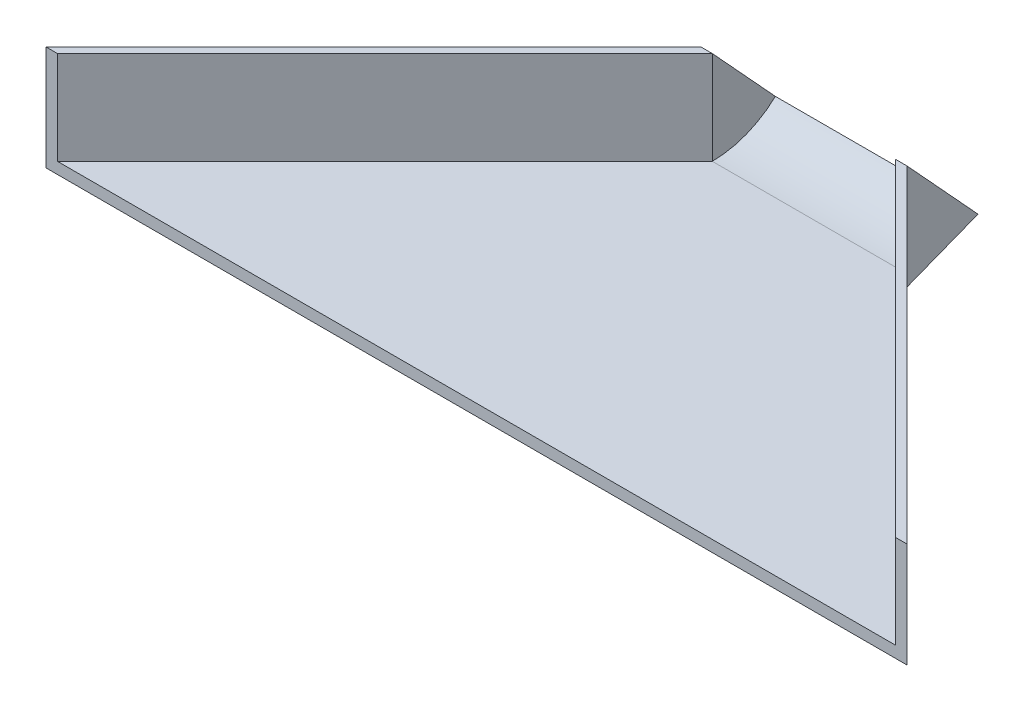
SolidWorks part; units mm, degrees
ref_plane "Front Plane" through (0, 0, 0) normal (0, 0, 1) x (1, 0, 0)
ref_plane "Top Plane" through (0, 0, 0) normal (0, 1, 0) x (1, 0, 0)
ref_plane "Right Plane" through (0, 0, 0) normal (1, 0, 0) x (0, 0, -1)
sketch "Sketch1" plane through (0, 0, 0) normal (0, 1, 0) x (1, 0, 0)
  line L0 (0, 0) -> (44.45, 0)
  line L1 (0, 0) -> (-79.375, -79.375)
  line L2 (44.45, 0) -> (123.825, -79.375)
  line L3 (-79.375, -79.375) -> (123.825, -79.375)
  dimension "D1" = 44.45
  dimension "D2" = 45
  dimension "D3" = 45
  dimension "D4" = 203.2
extrude "Boss-Extrude1" add sketch "Sketch1" along normal blind 2.7686
sketch "Sketch2" plane through (0, 2.7686, 0) normal (0, 1, 0) x (1, 0, 0)
  line L0 (0, 0) -> (-79.375, -79.375)
  line L2 (-82.1436, -79.375) -> (-2.7686, 0)
  line L3 (-2.7686, 0) -> (0, 0)
  line L4 (-82.1436, -79.375) -> (-79.375, -79.375)
  line L5 (44.45, 0) -> (47.2186, 0)
  line L6 (47.2186, 0) -> (126.5936, -79.375)
  line L7 (126.5936, -79.375) -> (123.825, -79.375)
  line L8 (44.45, 0) -> (123.825, -79.375)
  dimension "D1" = 2.7686
  dimension "D2" = 2.7686
  dimension "D3" = 2.7686
  dimension "D4" = 2.7686
extrude "Boss-Extrude2" add sketch "Sketch2" along normal blind 25.4 from surface at -2.7686 separate body starting at face at (22.225, 0, 39.6875)
ref_plane "Plane1" through (44.45, 0, 0) normal (1, 0, 0) x (0, 0, -1)
sketch "Sketch4" plane through (0, 0, 0) normal (0, 0, -1) x (-1, 0, 0)
  line L0 (-47.2186, 25.4) -> (-44.45, 25.4)
  line L1 (-44.45, 25.4) -> (-44.45, 0)
  line L2 (-44.45, 0) -> (-47.2186, 0)
  line L3 (-47.2186, 0) -> (-44.45, 0) construction
  line L4 (-47.2186, 25.4) -> (-47.2186, 0) construction
  line L5 (-47.2186, 0) -> (-47.2186, 25.4)
extrude "Boss-Extrude3" add sketch "Sketch4" along normal blind 25.4
sketch "Sketch5" plane through (47.2186, 0, 0) normal (1, 0, 0) x (0, 0, -1)
  line L0 (17.186, 6.6971) -> (0, 0)
  line L1 (0, 0) -> (25.4, 0)
  line L2 (25.4, 0) -> (25.4, 14.2449)
  line L3 (17.186, 6.6971) -> (176.1609, 152.7785) construction
  line L4 (25.4, 25.4) -> (25.4, 0) construction
  line L5 (25.4, 14.2449) -> (25.4, 25.4)
  line L6 (25.4, 25.4) -> (0, 25.4)
  line L7 (0, 25.4) -> (17.186, 6.6971)
extrude "Cut-Extrude1" cut sketch "Sketch5" against normal up to surface (2.7686 mm away) up to face at (44.45, 10.7137, -10.16)
sketch "Sketch10" plane through (44.45, 0, 0) normal (-1, 0, 0) x (0, 0, 1)
  line L0 (-17.186, 6.6971) -> (-15.2981, 8.7516)
  line L2 (-17.186, 6.6971) -> (0, 0)
  line L3 (0, 0) -> (0, 2.7686)
  arc A0 (0, 2.7686) -> (-15.2981, 8.7516) centre (0, 25.3182) cw
extrude "Boss-Extrude6" add sketch "Sketch10" along normal up to surface (44.45 mm away)
sketch "Sketch11" plane through (0, 0, 0) normal (-1, 0, 0) x (0, 0, 1)
  line L0 (0, 0) -> (0, 25.4)
  line L1 (0, 25.4) -> (-17.186, 6.6971)
  line L2 (-17.186, 6.6971) -> (0, 0)
extrude "Boss-Extrude7" add sketch "Sketch11" along normal up to surface (2.7686 mm away)
